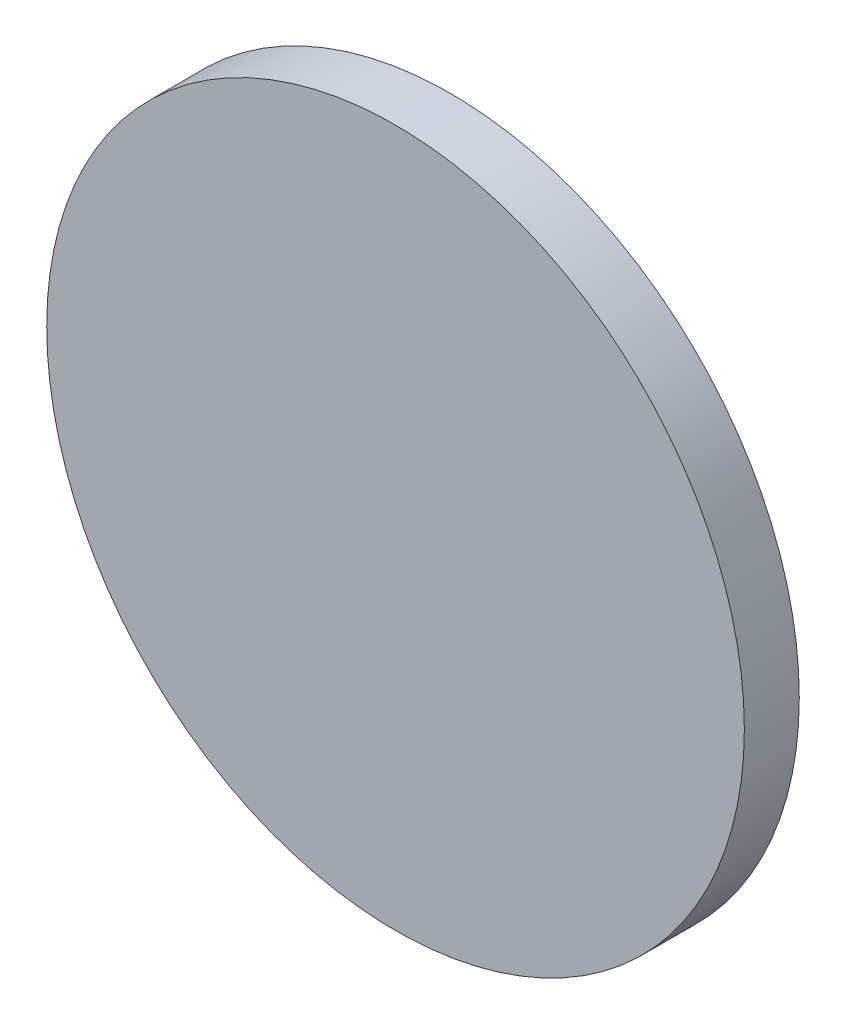
SolidWorks part; units mm, degrees
ref_plane "前视基准面" through (0, 0, 0) normal (0, 0, 1) x (1, 0, 0)
ref_plane "上视基准面" through (0, 0, 0) normal (0, 1, 0) x (1, 0, 0)
ref_plane "右视基准面" through (0, 0, 0) normal (1, 0, 0) x (0, 0, -1)
sketch "草图1" plane through (0, 0, 0) normal (0, 0, 1) x (1, 0, 0)
  circle A0 centre (0, 0) radius 12.7
  dimension "D1" = 25.4
extrude "凸台-拉伸1" add sketch "草图1" along normal blind 2 contours A0
